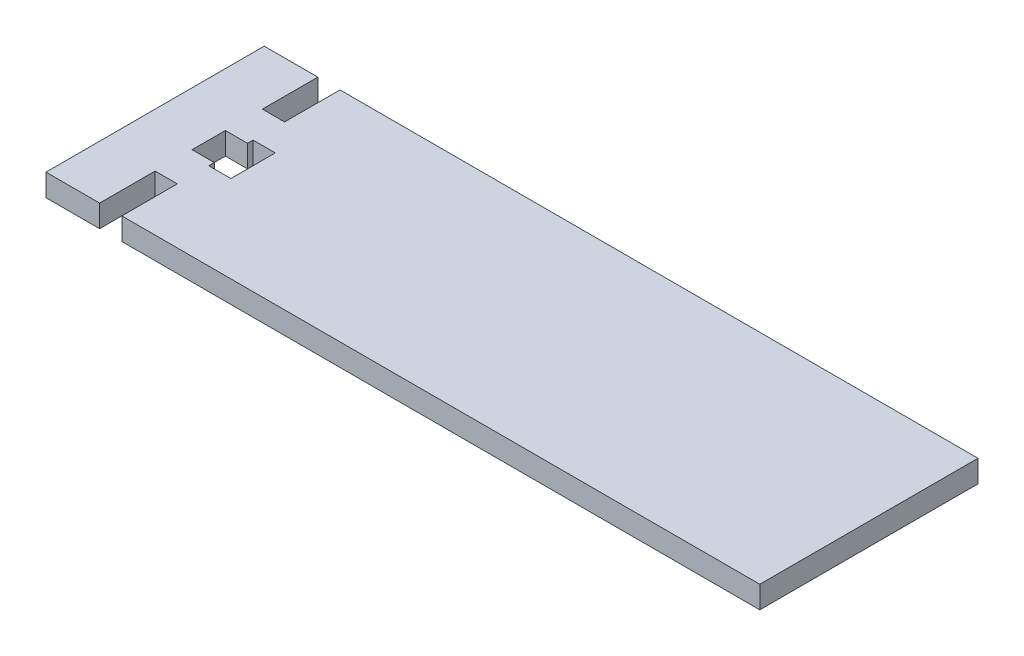
SolidWorks part; units mm, degrees
ref_plane "Front Plane" through (0, 0, 0) normal (0, 0, 1) x (1, 0, 0)
ref_plane "Top Plane" through (0, 0, 0) normal (0, 1, 0) x (1, 0, 0)
ref_plane "Right Plane" through (0, 0, 0) normal (1, 0, 0) x (0, 0, -1)
sketch "Sketch1" plane through (0, 0, 0) normal (0, 1, 0) x (1, 0, 0)
  line L1 (-96.5, 29.5) -> (96.5, 29.5)
  line L2 (-96.5, 29.5) -> (-96.5, -29.5)
  line L3 (-96.5, -29.5) -> (96.5, -29.5)
  line L4 (96.5, 29.5) -> (96.5, -29.5)
  line L5 (-96.5, 29.5) -> (96.5, -29.5) construction
  line L6 (-96.5, -29.5) -> (96.5, 29.5) construction
  point P0 (0, 0)
  dimension "D1" = 193
  dimension "D2" = 59
sketch "Sketch2" plane through (0, 0, 0) normal (0, 0, 1) x (1, 0, 0)
  line L0 (0, 0) -> (0, 6) construction
  line L1 (-96.5, 0) -> (96.5, 0) construction
  dimension "D1" = 6
extrude "Boss-Extrude1" add sketch "Sketch1" along normal up to vertex (6 mm away) contours L2 L3 L4 L1 up to point (0, 6, 0)
sketch "Sketch3" plane through (0, 0, 0) normal (0, -1, 0) x (-1, 0, 0)
  line L0 (96.5, 29.5) -> (96.5, -29.5) construction
  line L1 (76, 14.5) -> (82, 14.5)
  line L2 (76, 14.5) -> (76, 29.5)
  line L3 (76, 29.5) -> (82, 29.5)
  line L4 (82, 14.5) -> (82, 29.5)
  line L5 (76, -14.5) -> (82, -14.5)
  line L6 (76, -14.5) -> (76, -29.5)
  line L7 (76, -29.5) -> (82, -29.5)
  line L8 (82, -14.5) -> (82, -29.5)
  line L9 (82, -4.5) -> (76, -4.5)
  line L10 (82, -4.5) -> (82, 4.5)
  line L11 (82, 4.5) -> (76, 4.5)
  line L12 (76, -4.5) -> (76, 4.5)
  line L13 (82, -4.5) -> (76, -4.5) construction
  line L14 (128.7187, 75.3283) -> (128.7187, 87.3283) construction
  line L15 (70, 6) -> (76, 6)
  line L16 (70, 6) -> (70, -6)
  line L17 (70, -6) -> (76, -6)
  line L18 (76, 6) -> (76, -6)
  line L19 (76, -6) -> (70, -6) construction
extrude "Cut-Extrude1" cut sketch "Sketch3" against normal through all contours L5 L6 M3 M4 | L12 L9 L11 M4 | L18 L15 L16 L17 L12 | L2 L1 M4 M1
sketch "Sketch4" plane through (0, 0, 0) normal (0, -1, 0) x (1, 0, 0)
  line L0 (-76, -29.5) -> (96.5, -29.5) construction
  line L1 (-241.3298, -70.3283) -> (-42.2222, -70.3283)
  line L2 (-241.3298, -70.3283) -> (-241.3298, -29.5)
  line L3 (-241.3298, -29.5) -> (-42.2222, -29.5)
  line L4 (-42.2222, -70.3283) -> (-42.2222, -29.5)
  line L5 (-8.4444, -23.5) -> (-8.4444, -29.5) construction
  line L6 (-207.552, -70.3283) -> (-8.4444, -70.3283)
  line L7 (-207.552, -70.3283) -> (-207.552, -29.5)
  line L8 (-207.552, -29.5) -> (-8.4444, -29.5)
  line L9 (-8.4444, -70.3283) -> (-8.4444, -29.5)
  line L10 (-42.2222, -23.5) -> (-42.2222, -29.5) construction
extrude "Cut-Extrude2" cut sketch "Sketch4" against normal through all
mirror "Mirror1" about plane through (0, 0, 0) normal (0, 0, 1)
mirror "Mirror2" about plane through (0, 0, 0) normal (1, 0, 0)
equation "\"glass_width\"= 181"
equation "\"glass_height\"= 151"
equation "\"glass_thickness\"= 2.5"
equation "\"brood_space\"= 42"
equation "\"t1\"= 6"
equation "\"t2\"= 6"
equation "\"box_depth\"= \"brood_space\" + \"glass_thickness\" + \"glass_thickness\" + \"t2\" + \"t2\""
equation "\"box_width\"= \"glass_width\" + \"t1\" + \"t1\""
equation "\"food_height\"= 70"
equation "\"box_height\"= \"glass_height\" + ( \"t1\" * 3 ) + \"food_height\""
equation "\"D1@Sketch1\"=\"box_width\""
equation "\"D1@Sketch2\"=\"t1\""
equation "\"D2@Sketch1\"=\"box_depth\""
equation "\"entry_height\"= 24"
equation "\"entry_diameter\"= 8"
equation "\"food_top_clearance\"= 10"
equation "\"bar_width\"= 20"
equation "\"glassblocker_lower_height\"= 10"
equation "\"lower_edge_stickout\"=6"
